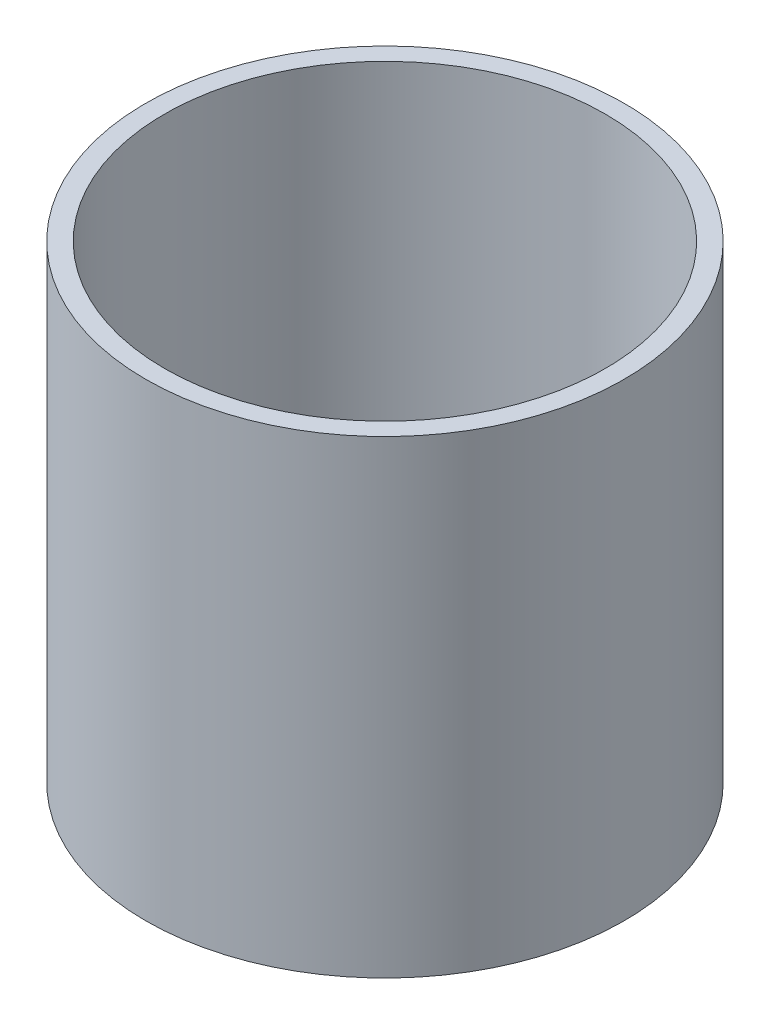
SolidWorks part; units mm, degrees
ref_plane "Front Plane" through (0, 0, 0) normal (0, 0, 1) x (1, 0, 0)
ref_plane "Top Plane" through (0, 0, 0) normal (0, 1, 0) x (1, 0, 0)
ref_plane "Right Plane" through (0, 0, 0) normal (1, 0, 0) x (0, 0, -1)
sketch "Sketch1" plane through (0, 0, 0) normal (0, 1, 0) x (1, 0, 0)
  circle A0 centre (0, 0) radius 23.5
  circle A1 centre (0, 0) radius 25.5
  dimension "D1" = 2
  dimension "D2" = 51
extrude "Boss-Extrude1" add sketch "Sketch1" along normal blind 50
